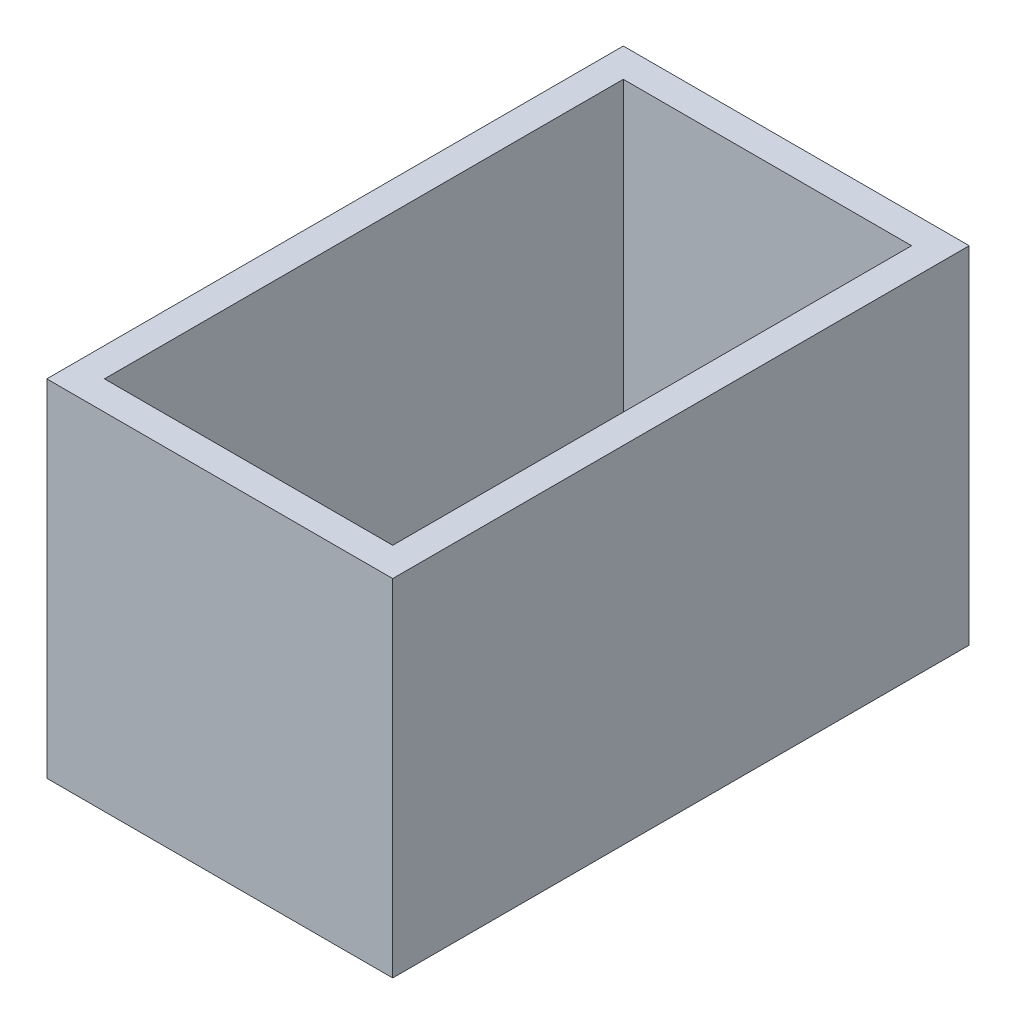
SolidWorks part; units mm, degrees
ref_plane "Front Plane" through (0, 0, 0) normal (0, 0, 1) x (1, 0, 0)
ref_plane "Top Plane" through (0, 0, 0) normal (0, 1, 0) x (1, 0, 0)
ref_plane "Right Plane" through (0, 0, 0) normal (1, 0, 0) x (0, 0, -1)
sketch "Sketch1" plane through (0, 0, 0) normal (0, 1, 0) x (1, 0, 0)
  line L1 (0, 127) -> (76.2, 127)
  line L2 (0, 127) -> (0, 0)
  line L3 (0, 0) -> (76.2, 0)
  line L4 (76.2, 127) -> (76.2, 0)
  point P4 (0, 0)
  dimension "D1" = 76.2
  dimension "D2" = 127
extrude "Boss-Extrude1" add sketch "Sketch1" along normal blind 76.2
shell "Shell1" thickness 6.35
equation "\"length\"= 3"
equation "\"width\"= 5"
equation "\"height\" = 3'materia"
equation "\"material\" = IIF ( \"height\" < 3in , .125 , .25 )"
equation "\"D1@Sketch1\"=\"length\""
equation "\"D2@Sketch1\"=\"width\""
equation "\"D1@Boss-Extrude1\"=\"height\""
equation "\"D1@Shell1\"=\"material\""
